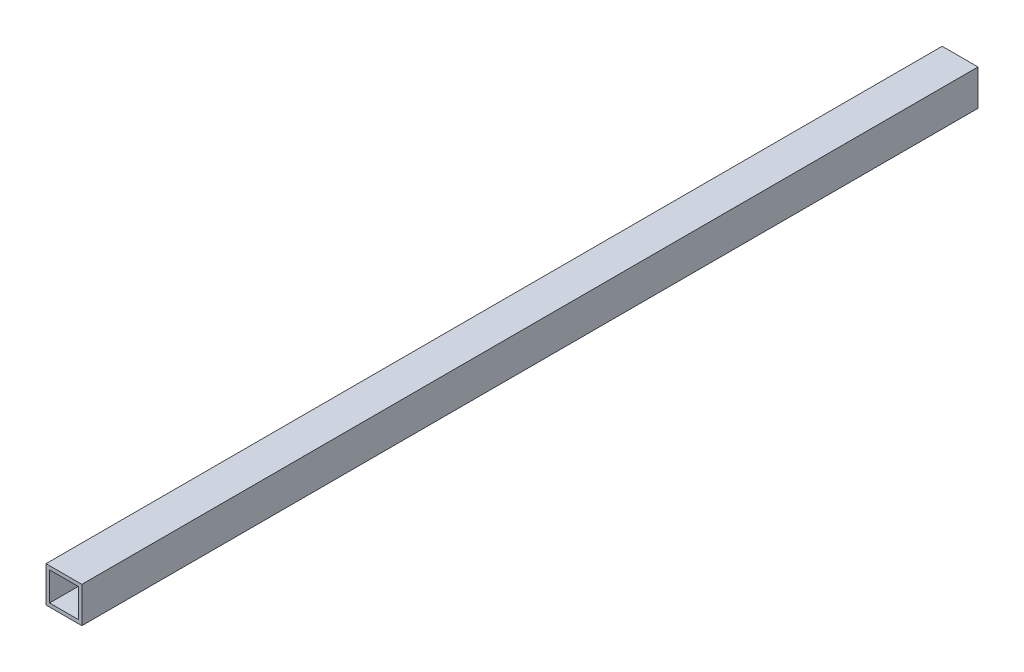
SolidWorks part; units mm, degrees
material "6061 Alloy"
ref_plane "Front Plane" through (0, 0, 0) normal (0, 0, 1) x (1, 0, 0)
ref_plane "Top Plane" through (0, 0, 0) normal (0, 1, 0) x (1, 0, 0)
ref_plane "Right Plane" through (0, 0, 0) normal (1, 0, 0) x (0, 0, -1)
sketch "Sketch1" plane through (0, 0, 0) normal (0, 0, 1) x (1, 0, 0)
  line L0 (-8, 8) -> (8, 8)
  line L1 (-10, -10) -> (10, -10)
  line L2 (-10, -10) -> (-10, 10)
  line L3 (-10, 10) -> (10, 10)
  line L4 (10, -10) -> (10, 10)
  line L5 (-10, -10) -> (10, 10) construction
  line L6 (-10, 10) -> (10, -10) construction
  line L7 (8, -8) -> (8, 8)
  line L8 (-8, -8) -> (8, -8)
  line L9 (-8, -8) -> (-8, 8)
  point P0 (0, 0)
  dimension "D1" = 20
  dimension "D2" = 20
  dimension "D3" = 2
extrude "Boss-Extrude1" add sketch "Sketch1" along normal blind 500
sketch "Sketch2" plane through (0, -10, 0) normal (0, 1, 0) x (1, 0, 0)
  line L0 (-10, -250) -> (10, -250) construction
  line L1 (-10, -500) -> (-10, 0) construction
  line L2 (10, -500) -> (10, 0) construction
  line L3 (-10, -110) -> (10, -110) construction
  line L4 (-10, -390) -> (10, -390) construction
  dimension "D1" = 140
